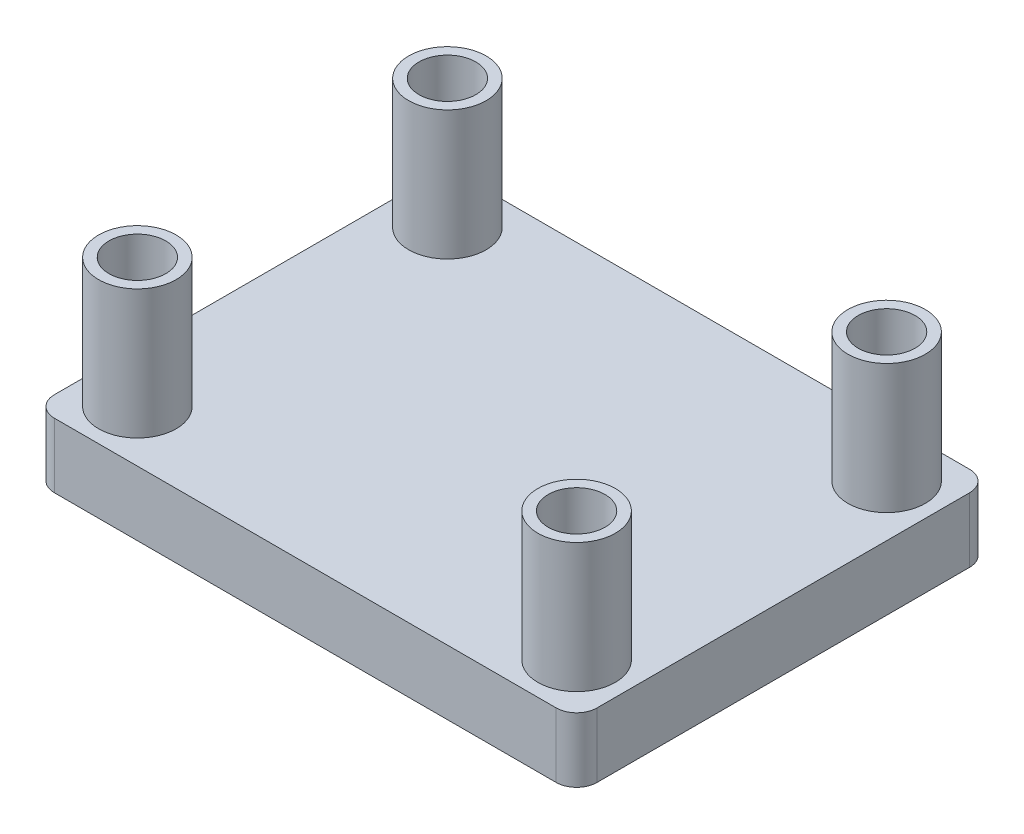
SolidWorks part; units mm, degrees
ref_plane "Front" through (0, 0, 0) normal (0, 0, 1) x (1, 0, 0)
ref_plane "Top" through (0, 0, 0) normal (0, 1, 0) x (1, 0, 0)
ref_plane "Right" through (0, 0, 0) normal (1, 0, 0) x (0, 0, -1)
sketch "Sketch1" plane through (0, 0, 0) normal (0, 1, 0) x (1, 0, 0)
  line L1 (-23.7864, 11.5944) -> (2.8836, 11.5944)
  line L2 (-23.7864, 11.5944) -> (-23.7864, -8.7256)
  line L3 (-23.7864, -8.7256) -> (2.8836, -8.7256)
  line L4 (2.8836, 11.5944) -> (2.8836, -8.7256)
  dimension "D1" = 20.32
  dimension "D2" = 26.67
extrude "Boss-Extrude1" add sketch "Sketch1" along normal blind 3.175
sketch "Sketch2" plane through (0, 3.175, 0) normal (0, 1, 0) x (1, 0, 0)
  line L0 (-23.7864, 11.5944) -> (-23.7864, -8.7256) construction
  line L2 (2.8836, 11.5944) -> (-23.7864, 11.5944) construction
  line L3 (2.8836, -8.7256) -> (2.8836, 11.5944) construction
  line L4 (-23.7864, 1.4344) -> (2.8836, 1.4344) construction
  circle A0 centre (-21.2464, 9.0544) radius 1.905
  circle A1 centre (-21.2464, 9.0544) radius 1.397
  circle A2 centre (0.3436, 9.0544) radius 1.905
  circle A3 centre (0.3436, 9.0544) radius 1.905
  circle A4 centre (0.3436, 9.0544) radius 1.397
  circle A5 centre (0.3436, -6.1856) radius 1.397
  circle A6 centre (0.3436, -6.1856) radius 1.905
  circle A7 centre (0.3436, -6.1856) radius 1.905
  circle A8 centre (-21.2464, -6.1856) radius 1.397
  circle A9 centre (-21.2464, -6.1856) radius 1.905
  dimension "D3" = 3.81
  dimension "D4" = 2.794
  dimension "D5" = 3.81
  dimension "D6" = 2.794
  dimension "D1" = 2.54
  dimension "D2" = 2.54
  dimension "D7" = 2.54
  dimension "D8" = 2.54
extrude "Boss-Extrude2" add sketch "Sketch2" along normal blind 6.35 contours A0 A1 | A2 A4 | A5 | A8 | A9 | A6
fillet "Fillet1" radius 1 4 edges at (-23.7864, 1.5875, -11.5944) (-23.7864, 1.5875, 8.7256) (2.8836, 1.5875, -11.5944) (2.8836, 1.5875, 8.7256)
